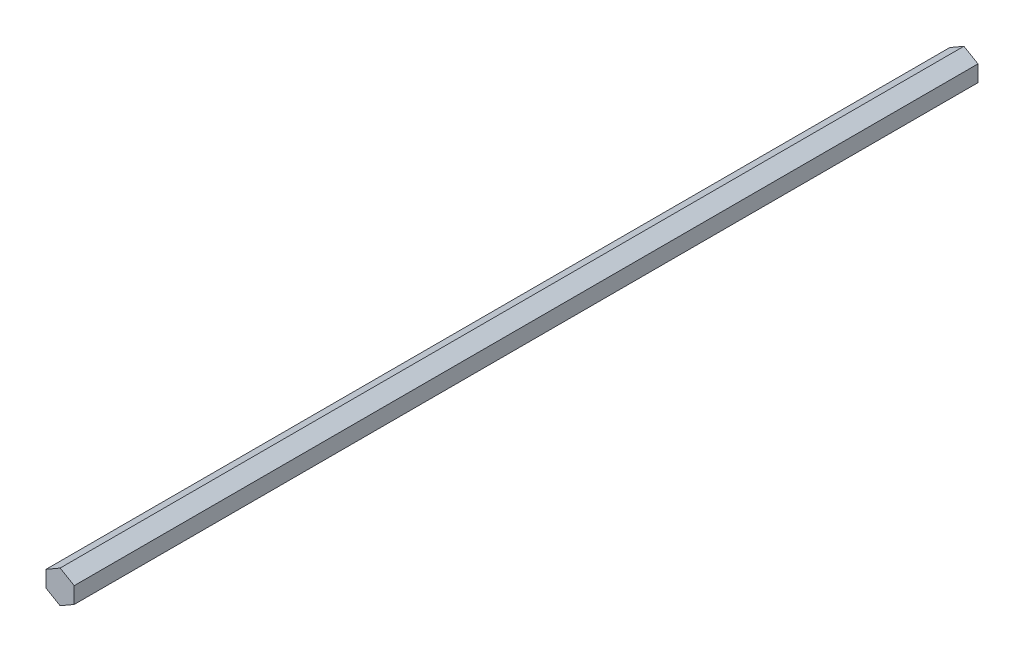
SolidWorks part; units mm, degrees
ref_plane "Front Plane" through (0, 0, 0) normal (0, 0, 1) x (1, 0, 0)
ref_plane "Top Plane" through (0, 0, 0) normal (0, 1, 0) x (1, 0, 0)
ref_plane "Right Plane" through (0, 0, 0) normal (1, 0, 0) x (0, 0, -1)
sketch "Sketch1" plane through (0, 0, 0) normal (0, 0, 1) x (1, 0, 0)
  line L1 (0, -7.3323) -> (6.35, -3.6662)
  line L2 (6.35, -3.6662) -> (6.35, 3.6662)
  line L3 (6.35, 3.6662) -> (0, 7.3323)
  line L4 (0, 7.3323) -> (-6.35, 3.6662)
  line L5 (-6.35, 3.6662) -> (-6.35, -3.6662)
  line L6 (-6.35, -3.6662) -> (0, -7.3323)
  circle A0 centre (0, 0) radius 6.35 construction
  dimension "D1" = 12.7
extrude "Boss-Extrude1" add sketch "Sketch1" along normal mid plane 406.4
